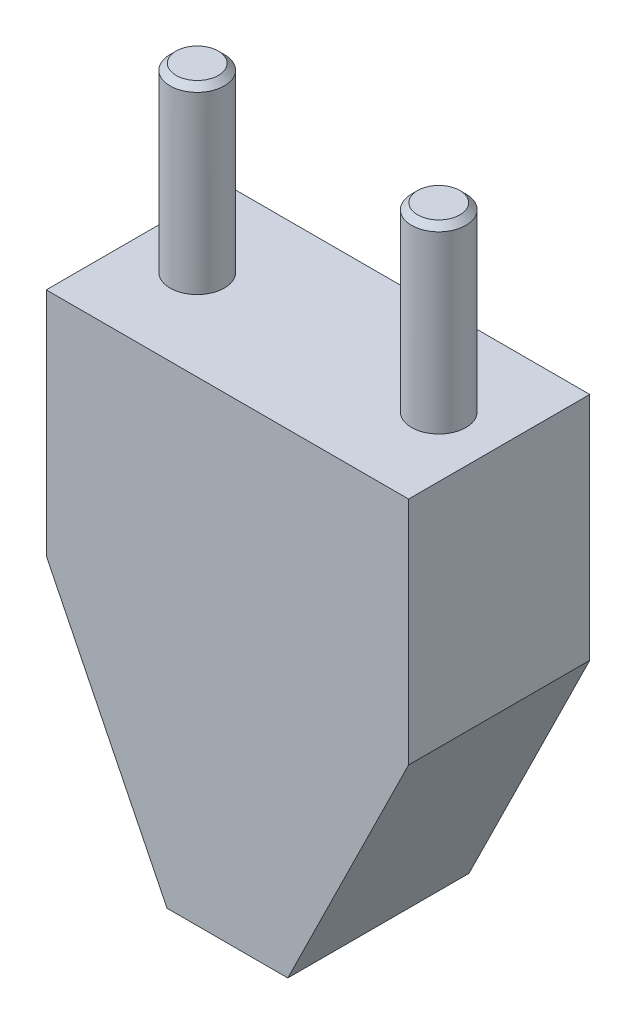
SolidWorks part; units mm, degrees
ref_plane "Front Plane" through (0, 0, 0) normal (0, 0, 1) x (1, 0, 0)
ref_plane "Top Plane" through (0, 0, 0) normal (0, 1, 0) x (1, 0, 0)
ref_plane "Right Plane" through (0, 0, 0) normal (1, 0, 0) x (0, 0, -1)
sketch "Sketch1" plane through (0, 0, 0) normal (0, 0, 1) x (1, 0, 0)
  line L0 (-21.2833, 0) -> (8.7167, 0)
  line L1 (8.7167, 0) -> (8.7167, -19.0695)
  line L2 (8.7167, -19.0695) -> (-1.2833, -39.3444)
  line L3 (-1.2833, -39.3444) -> (-11.2833, -39.3444)
  line L4 (-11.2833, -39.3444) -> (-21.2833, -19.0695)
  line L5 (-21.2833, -19.0695) -> (-21.2833, 0)
  dimension "D1" = 30
  dimension "D2" = 10
extrude "Boss-Extrude1" add sketch "Sketch1" along normal blind 15
sketch "Sketch2" plane through (0, 0, 0) normal (0, 1, 0) x (1, 0, 0)
  line L0 (-21.2833, -7.5) -> (8.7167, -7.5) construction
  line L1 (-21.2833, -15) -> (-21.2833, 0) construction
  line L2 (8.7167, -15) -> (8.7167, 0) construction
  line L3 (-6.2833, 0) -> (-6.2833, -15) construction
  line L4 (8.7167, 0) -> (-21.2833, 0) construction
  line L5 (8.7167, -15) -> (-21.2833, -15) construction
  circle A0 centre (-16.2833, -7.5) radius 2.25
  circle A1 centre (3.7167, -7.5) radius 2.25
  dimension "D1" = 4.5
  dimension "D2" = 4.5
  dimension "D3" = 10
  dimension "D4" = 10
extrude "Boss-Extrude2" add sketch "Sketch2" along normal blind 15
chamfer "Chamfer4" distance 0.5 angle 45 1 edges at (-18.5333, 15, 7.5)
chamfer "Chamfer5" distance 0.5 angle 45 1 edges at (1.4667, 15, 7.5)
sketch "Sketch4" plane through (0, -39.3444, 0) normal (0, -1, 0) x (-1, 0, 0)
  line L0 (6.2833, -15) -> (6.2833, 0) construction
  line L1 (11.2833, -15) -> (1.2833, -15) construction
  line L2 (11.2833, 0) -> (1.2833, 0) construction
  circle A0 centre (6.2833, -7.5) radius 3
extrude "Cut-Extrude1" cut sketch "Sketch4" against normal blind 5
